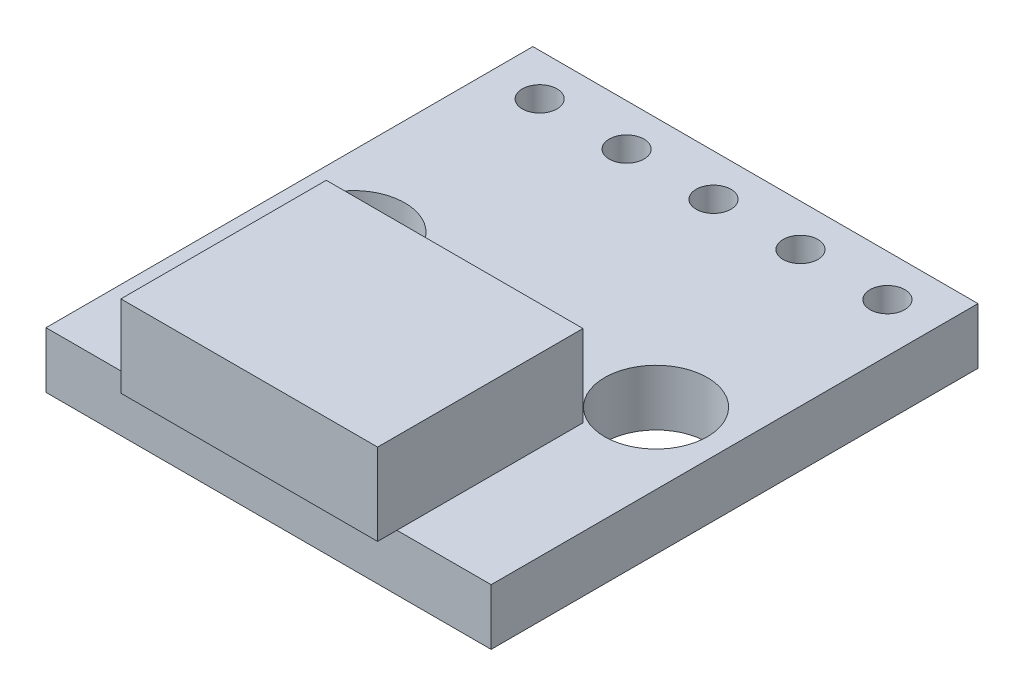
SolidWorks part; units mm, degrees
ref_plane "Front Plane" through (0, 0, 0) normal (0, 0, 1) x (1, 0, 0)
ref_plane "Top Plane" through (0, 0, 0) normal (0, 1, 0) x (1, 0, 0)
ref_plane "Right Plane" through (0, 0, 0) normal (1, 0, 0) x (0, 0, -1)
sketch "Sketch1" plane through (0, 0, 0) normal (0, 1, 0) x (1, 0, 0)
  line L0 (1.4224, 13) -> (3.9624, 13) construction
  line L1 (0, 0) -> (13.0048, 0)
  line L2 (0, 0) -> (0, 14.224)
  line L3 (0, 14.224) -> (13.0048, 14.224)
  line L4 (13.0048, 0) -> (13.0048, 14.224)
  line L5 (6.5024, 14.224) -> (6.5024, 0) construction
  line L6 (2.7524, 5.4356) -> (10.2524, 5.4356)
  line L7 (2.7524, 5.4356) -> (2.7524, -0.5644)
  line L8 (2.7524, -0.5644) -> (10.2524, -0.5644)
  line L9 (10.2524, 5.4356) -> (10.2524, -0.5644)
  circle A0 centre (1.4224, 13) radius 0.508
  circle A1 centre (3.9624, 13) radius 0.508
  circle A2 centre (6.5024, 13) radius 0.508
  circle A3 centre (9.0424, 13) radius 0.508
  circle A4 centre (11.5824, 13) radius 0.508
  circle A5 centre (2.0828, 6.9) radius 1.5
  circle A6 centre (10.922, 6.9) radius 1.5
  point P8 (6.5024, -0.5644)
  point P18 (6.5024, 0)
  point P29 (0.5828, 6.9)
  dimension "D3" = 1.016
  dimension "D10" = 3
  dimension "D1" = 13.0048
  dimension "D2" = 14.224
  dimension "D5" = 2.54
  dimension "D6" = 13
  dimension "D7" = 6
  dimension "D8" = 7.5
  dimension "D9" = 0.5644
  dimension "D11" = 6.9
  dimension "D12" = 8.8392
  dimension "D4" = 5
extrude "Boss-Extrude1" add sketch "Sketch1" along normal blind 1.6383 contours A5 | A0 | A1 | A2 | A3 | A4 | A6 | L1 L4 L3 L2
sketch "Sketch2" plane through (0, 1.6383, 0) normal (0, 1, 0) x (1, 0, 0)
  line L0 (2.7524, 5.4356) -> (10.2524, 5.4356) construction
  line L1 (10.2524, 5.4356) -> (10.2524, -0.5644) construction
  line L2 (2.7524, -0.5644) -> (10.2524, -0.5644) construction
  line L3 (2.7524, 5.4356) -> (2.7524, -0.5644) construction
  line L4 (2.7524, 5.4356) -> (10.2524, 5.4356)
  line L5 (10.2524, 5.4356) -> (10.2524, -0.5644)
  line L6 (2.7524, -0.5644) -> (10.2524, -0.5644)
  line L7 (2.7524, 5.4356) -> (2.7524, -0.5644)
extrude "Boss-Extrude3" add sketch "Sketch2" along normal blind 2.3876
